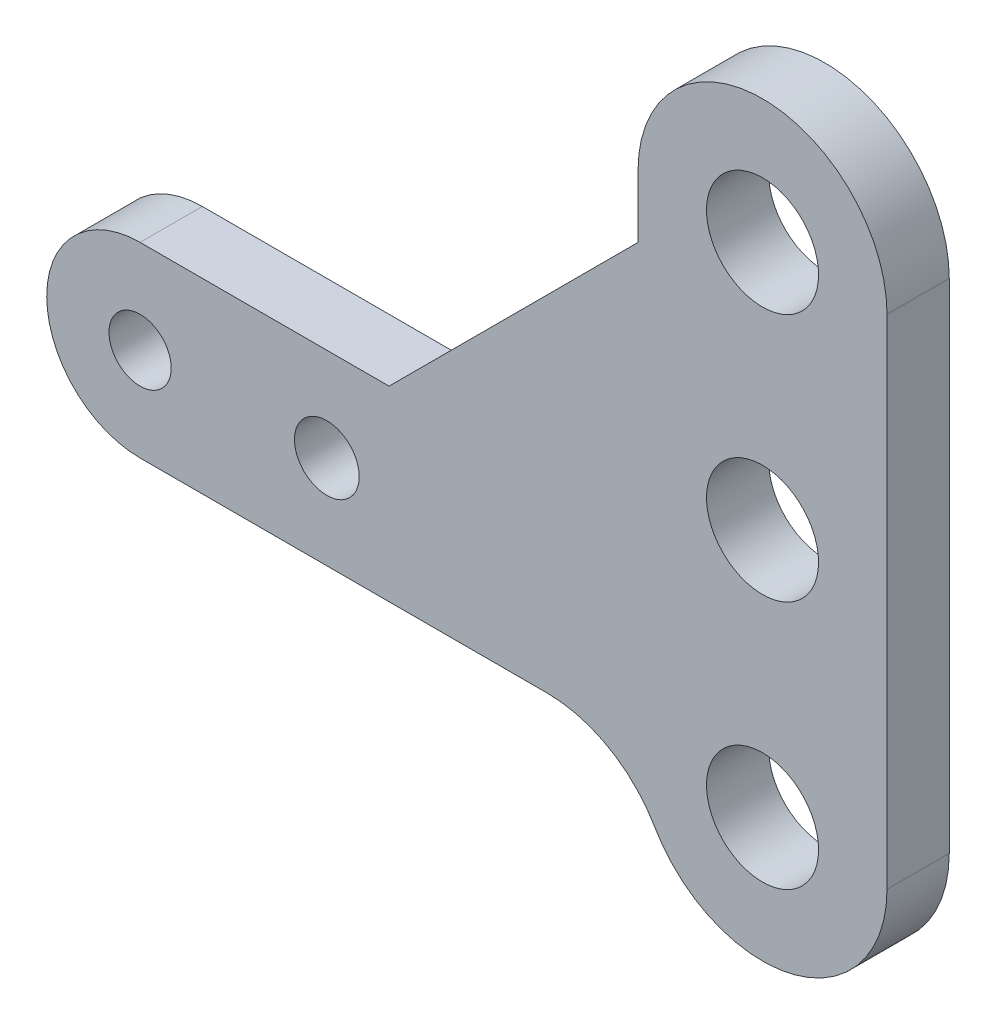
SolidWorks part; units mm, degrees
material "ABS"
ref_plane "前视基准面" through (0, 0, 0) normal (0, 0, 1) x (1, 0, 0)
ref_plane "上视基准面" through (0, 0, 0) normal (0, 1, 0) x (1, 0, 0)
ref_plane "右视基准面" through (0, 0, 0) normal (1, 0, 0) x (0, 0, -1)
sketch "草图1" plane through (0, 0, 0) normal (0, 0, 1) x (1, 0, 0)
  line L0 (0, 0) -> (-15, 0) construction
  line L1 (-15, 0) -> (0, 0) construction
  line L2 (-15, 7.5) -> (0, 7.5)
  line L3 (-15, -7.5) -> (0, -7.5)
  line L4 (0, 0) -> (15, 0) construction
  line L5 (0, 7.5) -> (15, 7.5)
  line L6 (0, -7.5) -> (15, -7.5)
  line L11 (15, 0) -> (35, 0) construction
  line L16 (35, 0) -> (35, 12.5) construction
  line L17 (35, 12.5) -> (35, 32.5) construction
  line L18 (35, 0) -> (35, -7.5) construction
  line L19 (15, -7.5) -> (25, -7.5)
  line L20 (45, -7.5) -> (45, 32.5)
  line L21 (25, 32.5) -> (25, 7.5)
  line L22 (25, 7.5) -> (15, 7.5)
  circle A0 centre (0, 0) radius 2.6
  circle A1 centre (-15, 0) radius 2.5
  arc A2 (-15, 7.5) -> (-15, -7.5) centre (-15, 0) ccw
  arc A3 (25, -7.5) -> (45, -7.5) centre (35, -7.5) ccw
  arc A4 (45, 32.5) -> (25, 32.5) centre (35, 32.5) ccw
  point P5 (-7.5, 0)
extrude "凸台-拉伸1" add sketch "草图1" against normal blind 5
sketch "草图2" plane through (0, 0, 0) normal (0, 0, 1) x (1, 0, 0)
  line L0 (35, 32.5) -> (35, 12.5) construction
  circle A0 centre (35, -7.5) radius 4.5
  circle A1 centre (35, 32.5) radius 4.5
  circle A2 centre (35, 12.5) radius 4.5
extrude "切除-拉伸1" cut sketch "草图2" against normal blind 10
chamfer "倒角1" distance 20 angle 45 1 edges at (25, 7.5, -2.5)
fillet "圆角1" radius 10 1 edges at (25, -7.5, -2.5)
